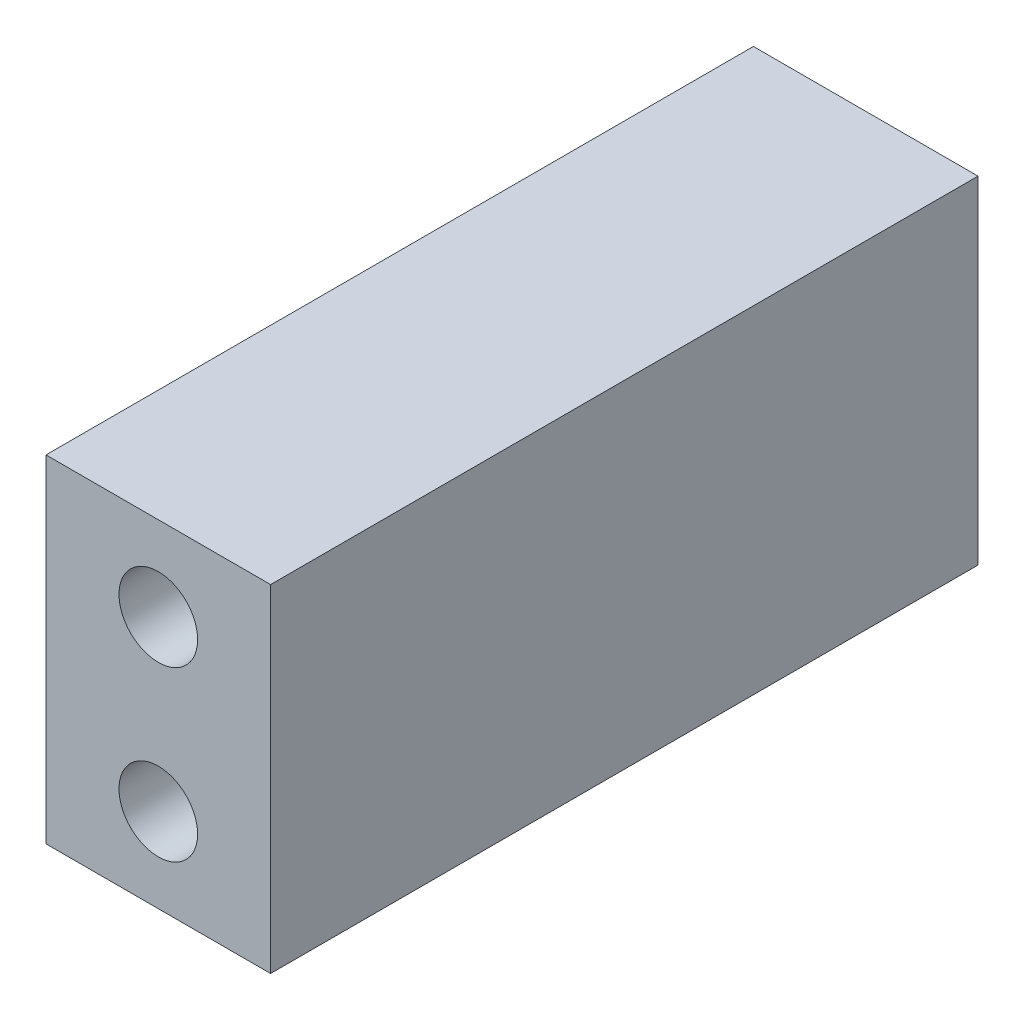
SolidWorks part; units mm, degrees
ref_plane "前视基准面" through (0, 0, 0) normal (0, 0, 1) x (1, 0, 0)
ref_plane "上视基准面" through (0, 0, 0) normal (0, 1, 0) x (1, 0, 0)
ref_plane "右视基准面" through (0, 0, 0) normal (1, 0, 0) x (0, 0, -1)
sketch "草图1" plane through (0, 0, 0) normal (0, 0, 1) x (1, 0, 0)
  line L0 (-16.6237, 0) -> (18.6224, 0) construction
  line L1 (-10, -15) -> (10, -15)
  line L2 (-10, -15) -> (-10, 15)
  line L3 (-10, 15) -> (10, 15)
  line L4 (10, -15) -> (10, 15)
  line L5 (-10, -15) -> (10, 15) construction
  line L6 (-10, 15) -> (10, -15) construction
  circle A0 centre (0, -7.5) radius 3.5
  circle A1 centre (0, 7.5) radius 3.5
  point P0 (0, 0)
  point P12 (0, 0)
  point P14 (-20.1824, 1.9672)
  dimension "D5" = 7
  dimension "D1" = 20
  dimension "D2" = 30
  dimension "D3" = 15
  dimension "D4" = 10
extrude "凸台-拉伸1" add sketch "草图1" along normal blind 63 contours L1 L4 L3 L2 A0 A1
